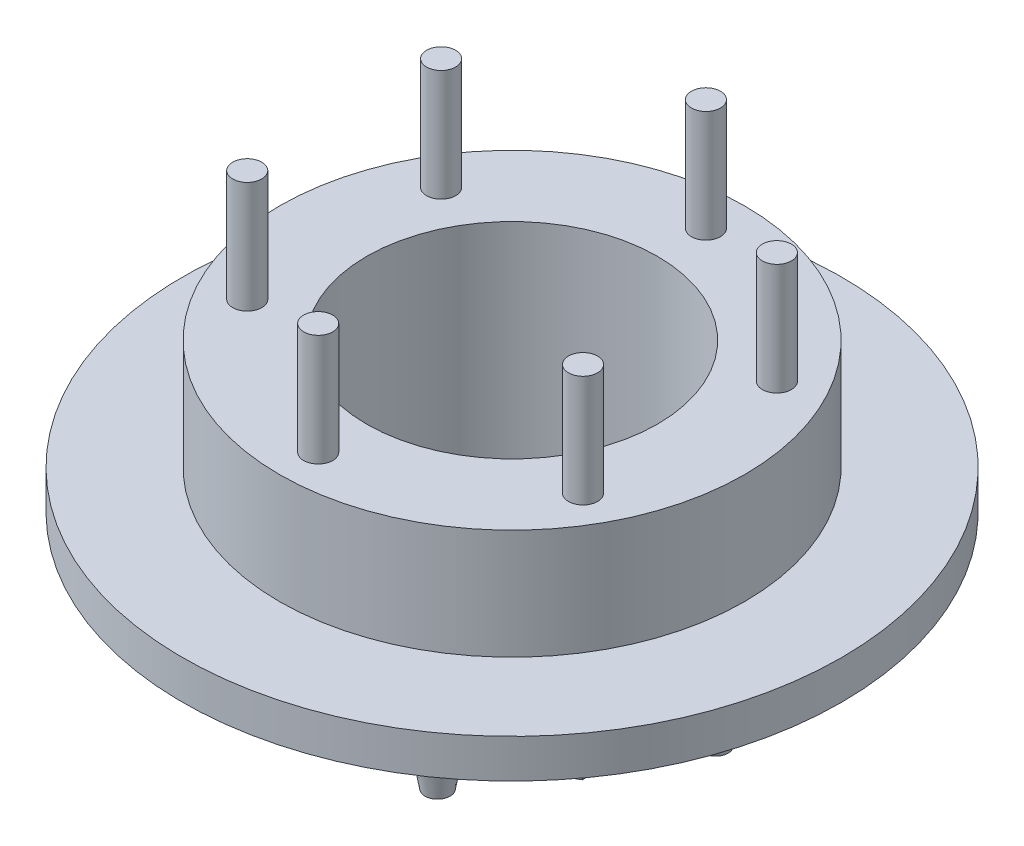
SolidWorks part; units mm, degrees
ref_plane "Front Plane" through (0, 0, 0) normal (0, 0, 1) x (1, 0, 0)
ref_plane "Top Plane" through (0, 0, 0) normal (0, 1, 0) x (1, 0, 0)
ref_plane "Right Plane" through (0, 0, 0) normal (1, 0, 0) x (0, 0, -1)
sketch "Sketch1" plane through (0, 0, 0) normal (0, 1, 0) x (1, 0, 0)
  circle A1 centre (0, 0) radius 12
  circle A2 centre (0, 0) radius 7.5
  dimension "D1" = 15
  dimension "D2" = 24
extrude "Boss-Extrude1" add sketch "Sketch1" along normal blind 10.875
sketch "Sketch2" plane through (0, 10.875, 0) normal (0, 1, 0) x (1, 0, 0)
  line L1 (0, 10) -> (-8.6603, 5) construction
  line L2 (-8.6603, 5) -> (-8.6603, -5) construction
  line L3 (-8.6603, -5) -> (0, -10) construction
  line L4 (0, -10) -> (8.6603, -5) construction
  line L5 (8.6603, -5) -> (8.6603, 5) construction
  line L6 (8.6603, 5) -> (0, 10) construction
  circle A0 centre (0, 0) radius 8.6603 construction
  circle A1 centre (0, 10) radius 0.75
  circle A2 centre (-8.6603, 5) radius 0.75
  circle A3 centre (-8.6603, -5) radius 0.75
  circle A4 centre (0, -10) radius 0.75
  circle A5 centre (8.6603, -5) radius 0.75
  circle A6 centre (8.6603, 5) radius 0.75
  dimension "D2" = 1.5
  dimension "D1" = 20
extrude "Boss-Extrude2" add sketch "Sketch2" along normal blind 5.75
sketch "Sketch3" plane through (0, 0, 0) normal (0, -1, 0) x (-1, 0, 0)
  line L1 (0, -9.9) -> (8.5737, -4.95)
  line L2 (8.5737, -4.95) -> (8.5737, 4.95)
  line L3 (8.5737, 4.95) -> (0, 9.9)
  line L4 (0, 9.9) -> (-8.5737, 4.95)
  line L5 (-8.5737, 4.95) -> (-8.5737, -4.95)
  line L6 (-8.5737, -4.95) -> (0, -9.9)
  circle A0 centre (0, 0) radius 8.5737 construction
  circle A1 centre (0, 0) radius 7.5
  circle A2 centre (0, 0) radius 7.5 construction
  dimension "D1" = 19.8
extrude "Boss-Extrude3" add sketch "Sketch3" along normal blind 2
sketch "Sketch4" plane through (0, 0, 0) normal (0, 0, 1) x (1, 0, 0)
  line L0 (12, 0) -> (12, 10.875) construction
  line L1 (12, 3.2) -> (17, 3.2)
  line L2 (12, 3.2) -> (12, 5.2)
  line L3 (12, 5.2) -> (17, 5.2)
  line L4 (17, 3.2) -> (17, 5.2)
  line L5 (8.5737, 0) -> (0, 0) construction
  line L6 (0, -2) -> (0, 6.6231) construction
  dimension "D1" = 3.2
  dimension "D2" = 2
  dimension "D3" = 5
revolve "Revolve1" add sketch "Sketch4" angle 360 about L6
sketch "Sketch5" plane through (0, 0, 0) normal (0, -1, 0) x (1, 0, 0)
  line L1 (5.25, 9.0933) -> (-5.25, 9.0933) construction
  line L2 (-5.25, 9.0933) -> (-10.5, 0) construction
  line L3 (-10.5, 0) -> (-5.25, -9.0933) construction
  line L4 (-5.25, -9.0933) -> (5.25, -9.0933) construction
  line L5 (5.25, -9.0933) -> (10.5, 0) construction
  line L6 (10.5, 0) -> (5.25, 9.0933) construction
  circle A0 centre (0, 0) radius 9.0933 construction
  circle A1 centre (-5.25, 9.0933) radius 1
  circle A2 centre (5.25, 9.0933) radius 1
  circle A3 centre (10.5, 0) radius 1
  circle A4 centre (5.25, -9.0933) radius 1
  circle A5 centre (-5.25, -9.0933) radius 1
  circle A6 centre (-10.5, 0) radius 1
  dimension "D2" = 2
  dimension "D1" = 21
extrude "Boss-Extrude4" add sketch "Sketch5" along normal blind 2 draft 10
